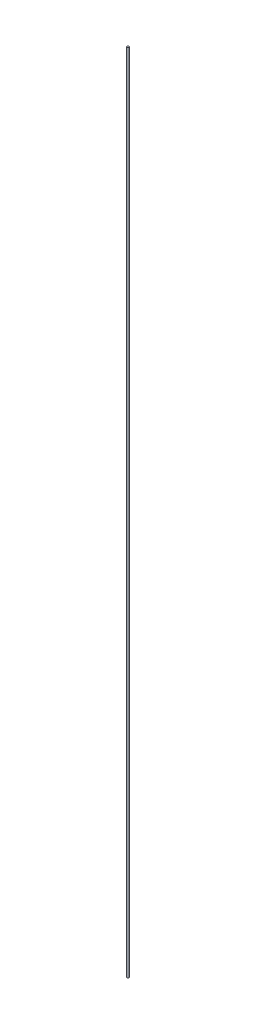
SolidWorks part; units mm, degrees
material "Hexcel AS4C (3000 Filaments)"
ref_plane "Front Plane" through (0, 0, 0) normal (0, 0, 1) x (1, 0, 0)
ref_plane "Top Plane" through (0, 0, 0) normal (0, 1, 0) x (1, 0, 0)
ref_plane "Right Plane" through (0, 0, 0) normal (1, 0, 0) x (0, 0, -1)
sketch "Sketch1" plane through (0, 0, 0) normal (0, 1, 0) x (1, 0, 0)
  circle A0 centre (0, 0) radius 1.27
  dimension "D1" = 2.54
extrude "Boss-Extrude1" add sketch "Sketch1" along normal blind 990.6
